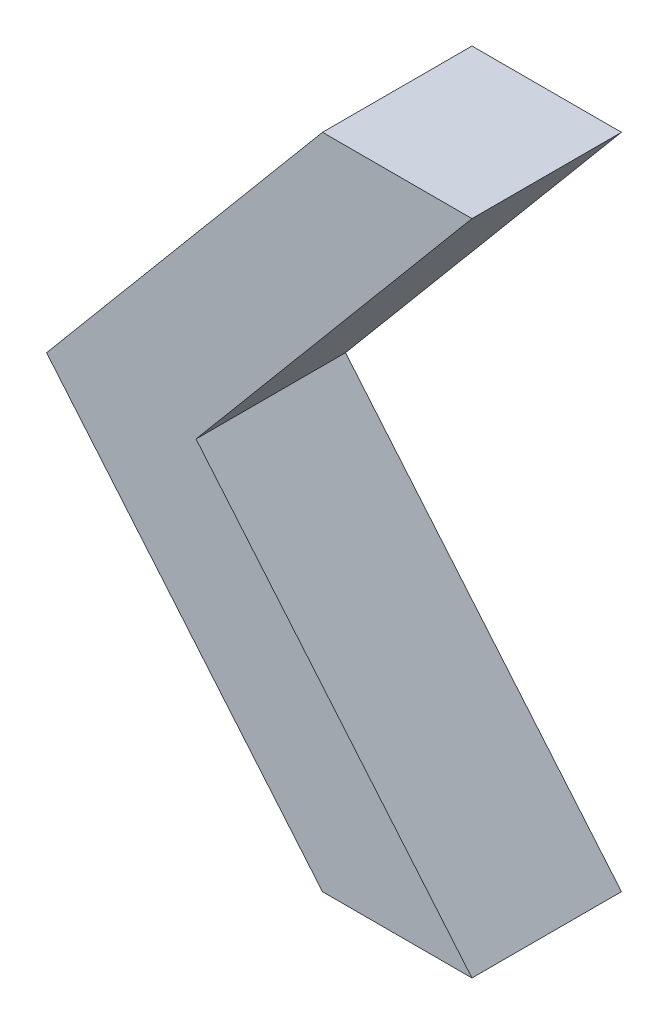
SolidWorks part; units mm, degrees
ref_plane "Front Plane" through (0, 0, 0) normal (0, 0, 1) x (1, 0, 0)
ref_plane "Top Plane" through (0, 0, 0) normal (0, 1, 0) x (1, 0, 0)
ref_plane "Right Plane" through (0, 0, 0) normal (1, 0, 0) x (0, 0, -1)
sketch "Sketch1" plane through (0, 0, 0) normal (0, 0, 1) x (1, 0, 0)
  line L0 (0, 0) -> (-23.0752, -27.5)
  line L1 (-23.0752, -27.5) -> (0, -55)
  line L2 (0, 0) -> (0, -90.5672) construction
  line L3 (0, 0) -> (12.5, 0)
  line L4 (0, -55) -> (12.5, -55)
  line L5 (12.5, 0) -> (-10.5752, -27.5)
  line L6 (-10.5752, -27.5) -> (12.5, -55)
  dimension "D1" = 100
  dimension "D2" = 55
  dimension "D3" = 12.5
  dimension "D4" = 12.5
extrude "Boss-Extrude1" add sketch "Sketch1" along normal blind 12.5
